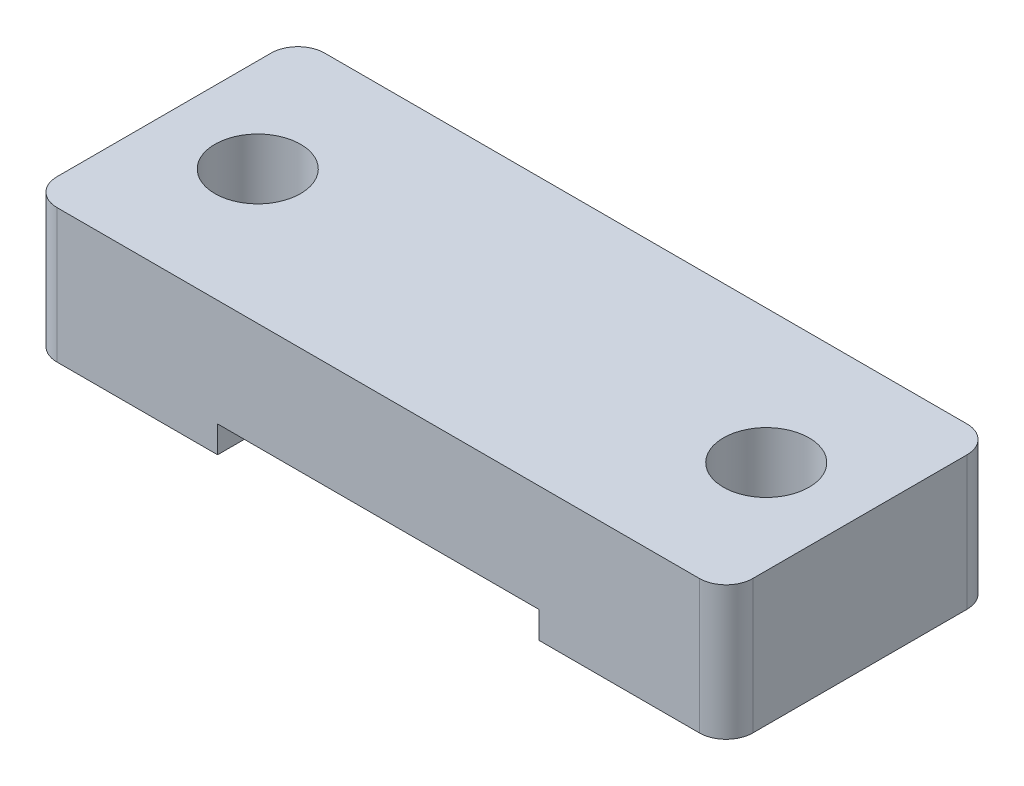
SolidWorks part; units mm, degrees
ref_plane "前视基准面" through (0, 0, 0) normal (0, 0, 1) x (1, 0, 0)
ref_plane "上视基准面" through (0, 0, 0) normal (0, 1, 0) x (1, 0, 0)
ref_plane "右视基准面" through (0, 0, 0) normal (1, 0, 0) x (0, 0, -1)
sketch "草图2" plane through (0, 0, 0) normal (0, 1, 0) x (1, 0, 0)
  line L1 (-13, 5) -> (13, 5)
  line L2 (-13, 5) -> (-13, -5)
  line L3 (-13, -5) -> (13, -5)
  line L4 (13, 5) -> (13, -5)
  line L5 (0, -5) -> (0, 5) construction
  line L6 (-13, 0) -> (13, 0) construction
  point P0 (0, 0)
  dimension "D1" = 10
  dimension "D2" = 26
extrude "凸台-拉伸1" add sketch "草图2" along normal blind 4
sketch "草图3" plane through (0, 0, 0) normal (0, -1, 0) x (1, 0, 0)
  line L0 (-13, 5) -> (13, 5) construction
  line L1 (13, -5) -> (6, -5)
  line L2 (13, -5) -> (13, 5)
  line L3 (13, 5) -> (6, 5)
  line L4 (6, -5) -> (6, 5)
  line L6 (-13, -5) -> (-6, -5)
  line L7 (-13, -5) -> (-13, 5)
  line L8 (-13, 5) -> (-6, 5)
  line L9 (-6, -5) -> (-6, 5)
  dimension "D1" = 7
  dimension "D2" = 7
extrude "凸台-拉伸2" add sketch "草图3" along normal blind 1
sketch "草图4" plane through (0, -1, 0) normal (0, -1, 0) x (1, 0, 0)
  line L0 (9.5, -5) -> (9.5, 5) construction
  line L1 (6, -5) -> (13, -5) construction
  line L2 (13, 5) -> (6, 5) construction
  line L3 (0, -11.158) -> (0, 8.2596) construction
  circle A0 centre (9.5, 0) radius 1.6
  circle A1 centre (-9.5, 0) radius 1.6
  dimension "D1" = 3.2
extrude "切除-拉伸1" cut sketch "草图4" against normal through all
fillet "圆角1" radius 1 4 edges at (13, 1.5, 5) (-13, 1.5, 5) (-13, 1.5, -5) (13, 1.5, -5)
